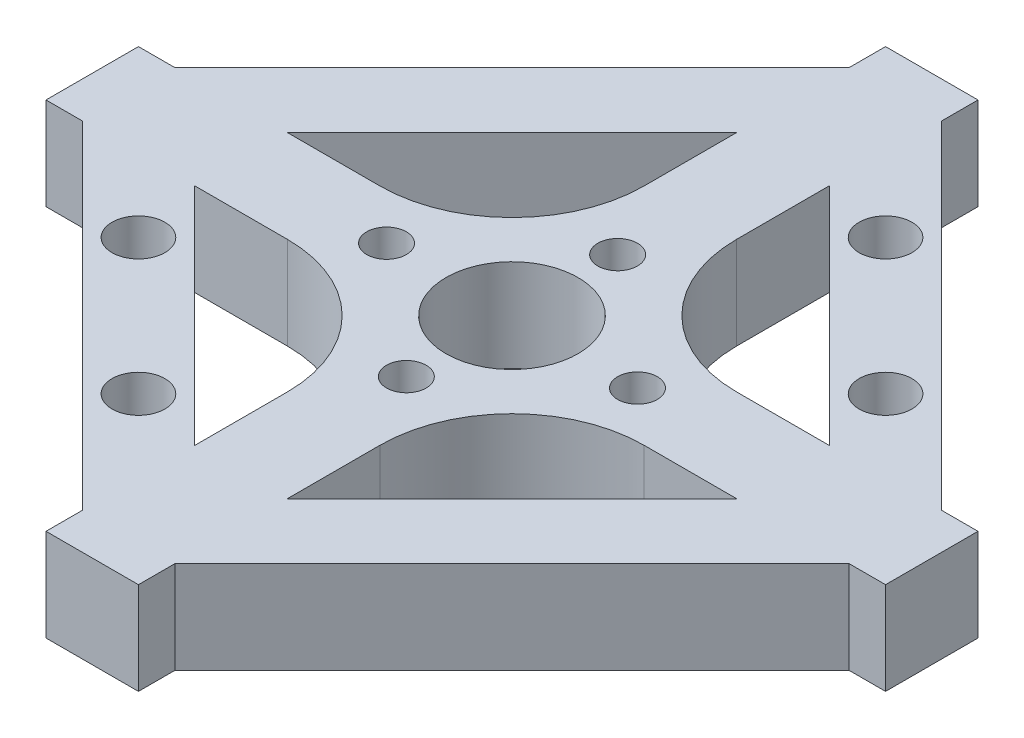
SolidWorks part; units mm, degrees
ref_plane "Front Plane" through (0, 0, 0) normal (0, 0, 1) x (1, 0, 0)
ref_plane "Top Plane" through (0, 0, 0) normal (0, 1, 0) x (1, 0, 0)
ref_plane "Right Plane" through (0, 0, 0) normal (1, 0, 0) x (0, 0, -1)
sketch "Sketch1" plane through (0, 0, 0) normal (0, 1, 0) x (1, 0, 0)
  line L0 (0, 0) -> (9.5, 0)
  line L1 (0, 0) -> (0, 5)
  line L2 (-3.5, -31.7843) -> (3.5, -31.7843)
  line L3 (-3.5, -31.7843) -> (-3.5, -29.0269)
  line L4 (3.5, -31.7843) -> (3.5, -29.0269)
  line L5 (-3.5, 31.7843) -> (3.5, 31.7843)
  line L6 (-3.5, -31.7843) -> (-3.2265, -29.3004) construction
  line L7 (3.5, -31.7843) -> (3.2265, -29.3004) construction
  line L8 (-31.7843, -3.5) -> (-31.7843, 3.5)
  line L9 (-31.7843, -3.5) -> (-29.0269, -3.5)
  line L10 (-31.7843, 3.5) -> (-27.5416, 3.5)
  line L11 (31.7843, -3.5) -> (31.7843, 3.5)
  line L12 (-31.7843, -3.5) -> (-29.3004, -3.2265) construction
  line L13 (-31.7843, 3.5) -> (-27.0166, 2.975) construction
  line L14 (0, 0) -> (12.0208, 12.0208)
  line L16 (29.3004, 3.2265) -> (3.2265, 29.3004)
  line L17 (27.5416, -3.5) -> (27.0166, -2.975)
  line L19 (-3.0792, -27.9625) -> (-3.5, -27.5416)
  line L20 (27.5416, -3.5) -> (27.1544, -2.9902) construction
  line L21 (2.975, 27.0166) -> (3.5, 31.7843) construction
  line L22 (0, 0) -> (-3.5355, 3.5355)
  line L23 (13.5, 3.5) -> (20.5416, 3.5)
  line L24 (3.5, -27.5416) -> (2.975, -27.0166)
  line L26 (-3.2265, -29.3004) -> (-29.3004, -3.2265)
  line L29 (3.2265, -29.3004) -> (29.3004, -3.2265)
  line L31 (-3.5, -27.5416) -> (-2.975, -27.0166)
  line L33 (3.0792, 27.9625) -> (3.5, 27.5416)
  line L34 (-29.3004, 3.2265) -> (-3.2265, 29.3004)
  line L35 (-31.7843, 0.7426) -> (-31.0416, 0)
  line L37 (-29.3004, -3.2265) -> (-3.2265, -29.3004)
  line L39 (-27.5416, 3.5) -> (-27.0166, 2.975)
  line L40 (-3.5, 27.5416) -> (-2.975, 27.0166)
  line L42 (3.2265, 29.3004) -> (29.3004, 3.2265)
  line L44 (3.0792, 27.9625) -> (3.5, 27.5416)
  line L45 (-3.2265, 29.3004) -> (-29.3004, 3.2265)
  line L46 (-31.7843, 0.7426) -> (-31.0416, 0)
  line L47 (3.5, 27.5416) -> (2.975, 27.0166)
  line L50 (29.3004, -3.2265) -> (3.2265, -29.3004)
  line L52 (-2.3848, 21.6568) -> (-21.6568, 2.3848)
  line L53 (2.975, 27.0166) -> (3.5, 27.5416)
  line L54 (2.3848, 21.6568) -> (21.6568, 2.3848)
  line L55 (-2.975, 27.0166) -> (-3.5, 27.5416)
  line L56 (-2.9902, 27.1544) -> (-3.5, 27.5416) construction
  line L57 (7.6014, 20.6829) -> (10.4298, 17.8544)
  line L58 (3.5, 27.5416) -> (3.5, 31.7843)
  line L59 (-3.2265, 29.3004) -> (-3.5, 31.7843) construction
  line L60 (13.5, -3.5) -> (20.5416, -3.5)
  line L61 (9.8094, 17.4329) -> (7.0342, 19.5407) construction
  line L62 (17.8544, 10.4298) -> (20.6829, 7.6014)
  line L63 (10.8513, 18.4749) -> (3.1508, 28.6136) construction
  line L64 (-3.0792, -27.9625) -> (-3.5, -27.5416)
  line L65 (29.0269, 3.5) -> (31.7843, 3.5)
  line L66 (29.3004, 3.2265) -> (31.7843, 3.5) construction
  line L67 (3.0792, -27.9625) -> (3.5, -27.5416)
  line L68 (24.52, 0.4784) -> (24.0416, 0)
  line L69 (3.0792, -27.9625) -> (3.5, -27.5416)
  line L70 (27.5416, 3.5) -> (27.0166, 2.975) [skipped]
  line L71 (21.2501, 8.7435) -> (18.4749, 10.8513) construction
  line L72 (22.225, 3.5) -> (17.4329, 9.8094) construction
  line L73 (27.9625, -3.0792) -> (27.5416, -3.5)
  line L74 (27.9625, -3.0792) -> (27.5416, -3.5)
  line L75 (29.3004, -3.2265) -> (31.7843, -3.5) construction
  line L76 (29.0269, -3.5) -> (31.7843, -3.5)
  line L77 (27.0166, -2.975) -> (27.9625, -3.0792) construction
  line L78 (21.6568, 2.3848) -> (2.3848, 21.6568)
  line L79 (27.0166, -2.975) -> (27.5416, -3.5)
  line L80 (24.52, 0.4784) -> (22.9628, 2.5286) construction
  line L81 (3.5, -3.5707) -> (3.5, 3.5707)
  line L82 (0.5473, -4.97) -> (-0.5473, 4.97) construction
  line L83 (-0.5473, -4.97) -> (0.5473, 4.97) construction
  line L84 (2.975, -27.0166) -> (3.5, -27.5416)
  line L85 (-3.5, -20.5416) -> (-21.6568, -2.3848)
  line L86 (-2.975, -27.0166) -> (-3.5, -27.5416)
  line L87 (2.3848, -21.6568) -> (21.6568, -2.3848)
  line L88 (-2.3848, -21.6568) -> (-0.7371, -6.6936) construction
  line L89 (-3.0792, -27.9625) -> (-2.975, -27.0166) construction
  line L90 (-3.5, -24.7843) -> (-3.5, -13.5)
  line L91 (3.0792, -27.9625) -> (0.7371, -6.6936) construction
  line L92 (3.5, -20.5416) -> (3.5, -13.5)
  line L93 (-10.4298, -17.8544) -> (-2.8056, -25.4786)
  line L94 (-25.4786, -2.8056) -> (-17.8544, -10.4298)
  line L95 (-21.6568, 2.3848) -> (-2.3848, 21.6568)
  line L96 (-3.5, -3.5707) -> (-3.5, 3.5707)
  line L97 (-25.4786, -2.8056) -> (-8.3116, -0.9153) construction
  line L98 (-24.7843, -3.5) -> (-13.5, -3.5)
  line L99 (-27.5416, -3.5) -> (-27.0166, -2.975) [skipped]
  line L100 (-27.9625, -3.0792) -> (-27.0166, -2.975) construction
  line L101 (-27.9625, 3.0792) -> (-27.5416, 3.5)
  line L102 (-27.9625, 3.0792) -> (-27.5416, 3.5)
  line L103 (-27.0166, 2.975) -> (-27.5416, 3.5)
  line L104 (-21.6568, -2.3848) -> (-3.5, -20.5416)
  line L105 (-21.6568, 2.3848) -> (-8.3116, 0.9153) construction
  line L106 (-20.5416, 3.5) -> (-13.5, 3.5)
  line L107 (24.0416, 0) -> (24.52, 0.4784)
  line L108 (21.6568, -2.3848) -> (2.3848, -21.6568)
  line L109 (-3.5707, -3.5) -> (3.5707, -3.5)
  line L110 (-4.97, -0.5473) -> (21.6568, 2.3848) construction
  line L111 (-4.97, 0.5473) -> (21.6568, -2.3848) construction
  line L112 (-3.5707, 3.5) -> (3.5707, 3.5)
  line L113 (-6.4289, 6.4289) -> (-10.6066, 10.6066)
  line L114 (-3.5, 13.5) -> (-3.5, 31.7843)
  line L115 (-0.7371, 6.6936) -> (-2.9902, 27.1544) construction
  line L116 (0, 6.5) -> (0, 8)
  line L117 (0.7371, 6.6936) -> (2.3848, 21.6568) construction
  line L118 (3.5, 13.5) -> (3.5, 20.5416)
  circle A0 centre (0, 0) radius 5
  circle A1 centre (0, 8) radius 1.5
  circle A2 centre (9.5, 0) radius 1.5
  circle A3 centre (0, -8) radius 1.5
  circle A4 centre (-9.5, 0) radius 1.5
  arc A5 (-13.5, 3.5) -> (-3.5, 13.5) centre (-13.5, 13.5) ccw
  arc A6 (3.5, 13.5) -> (13.5, 3.5) centre (13.5, 13.5) ccw
  arc A7 (13.5, -3.5) -> (3.5, -13.5) centre (13.5, -13.5) ccw
  arc A8 (-3.5, -13.5) -> (-13.5, -3.5) centre (-13.5, -13.5) ccw
  circle A9 centre (9.0156, 19.2687) radius 2
  circle A10 centre (19.2687, 9.0156) radius 2
  circle A11 centre (-19.2687, -9.0156) radius 2
  circle A12 centre (-9.0156, -19.2687) radius 2
  point P34 (0, 0)
  point P81 (0, 0)
  point P82 (0, 0)
  dimension "D1" = 10
  dimension "D4" = 3
  dimension "D5" = 3
  dimension "D8" = 45
  dimension "D9" = 4
  dimension "D15" = 4
  dimension "D16" = 3
  dimension "D17" = 14.5
  dimension "D2" = 9.5
  dimension "D3" = 8
  dimension "D6" = 7
  dimension "D7" = 7
  dimension "D10" = 10
  dimension "D11" = 10
  dimension "D12" = 0
  dimension "D19" = 90
  dimension "D20" = 15
  dimension "D21" = 4
  dimension "D13" = 4
extrude "Boss-Extrude1" add sketch "Sketch1" along normal blind 7
